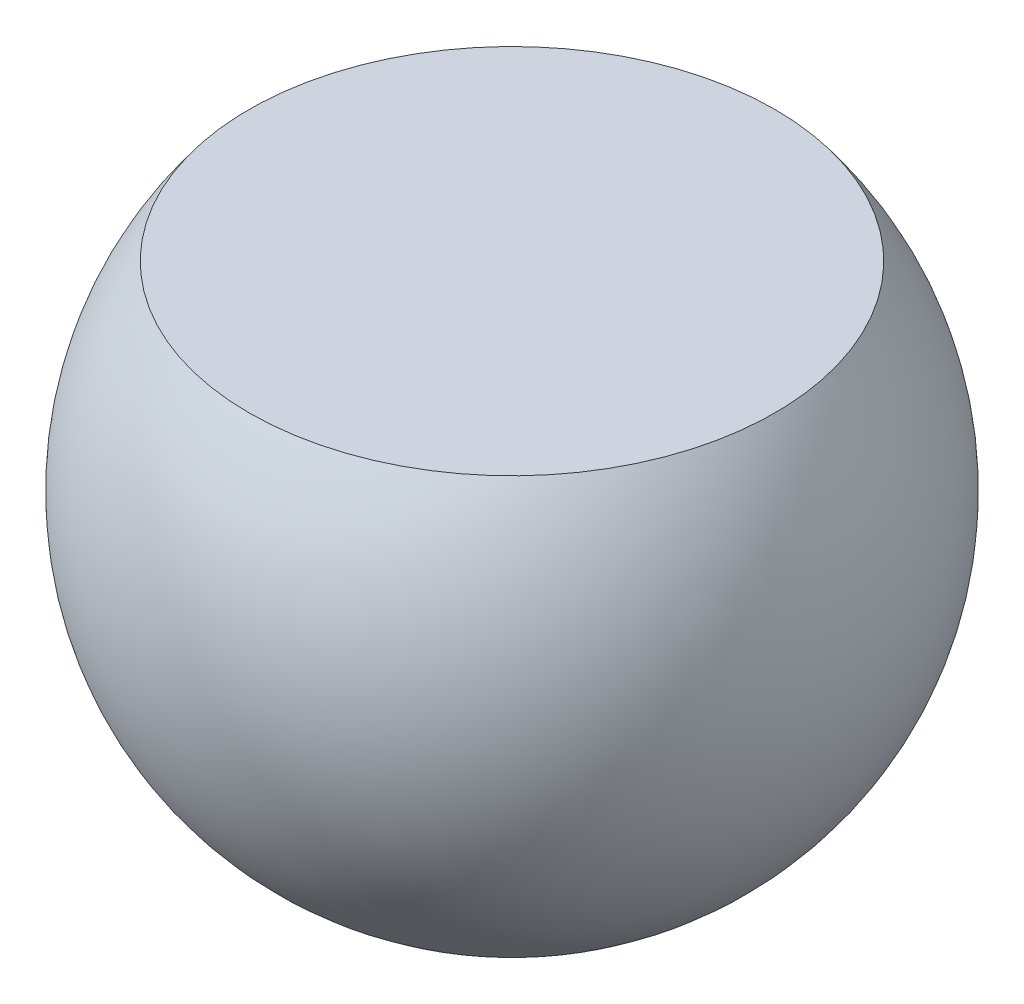
SolidWorks part; units mm, degrees
ref_plane "Front Plane" through (0, 0, 0) normal (0, 0, 1) x (1, 0, 0)
ref_plane "Top Plane" through (0, 0, 0) normal (0, 1, 0) x (1, 0, 0)
ref_plane "Right Plane" through (0, 0, 0) normal (1, 0, 0) x (0, 0, -1)
sketch "Sketch1" plane through (0, 0, 0) normal (0, 1, 0) x (1, 0, 0)
  line L0 (0, 1.6825) -> (0, -1.6825)
  arc A0 (0, 1.6825) -> (0, -1.6825) centre (0, 0) ccw
  dimension "D1" = 3.365
revolve "Revolve2" add sketch "Sketch1" angle 360 about L0
ref_plane "Plane1" through (0, 1.016, 0) normal (0, 1, 0) x (1, 0, 0)
sketch "Sketch3" plane through (0, 1.016, 0) normal (0, 1, 0) x (1, 0, 0)
  line L1 (4.216, 4.1288) -> (-4.216, 4.1288)
  line L2 (4.216, 4.1288) -> (4.216, -4.1288)
  line L3 (4.216, -4.1288) -> (-4.216, -4.1288)
  line L4 (-4.216, 4.1288) -> (-4.216, -4.1288)
  line L5 (4.216, 4.1288) -> (-4.216, -4.1288) construction
  line L6 (4.216, -4.1288) -> (-4.216, 4.1288) construction
  point P0 (0, 0)
extrude "Cut-Extrude1" cut sketch "Sketch3" along normal blind 2.54
